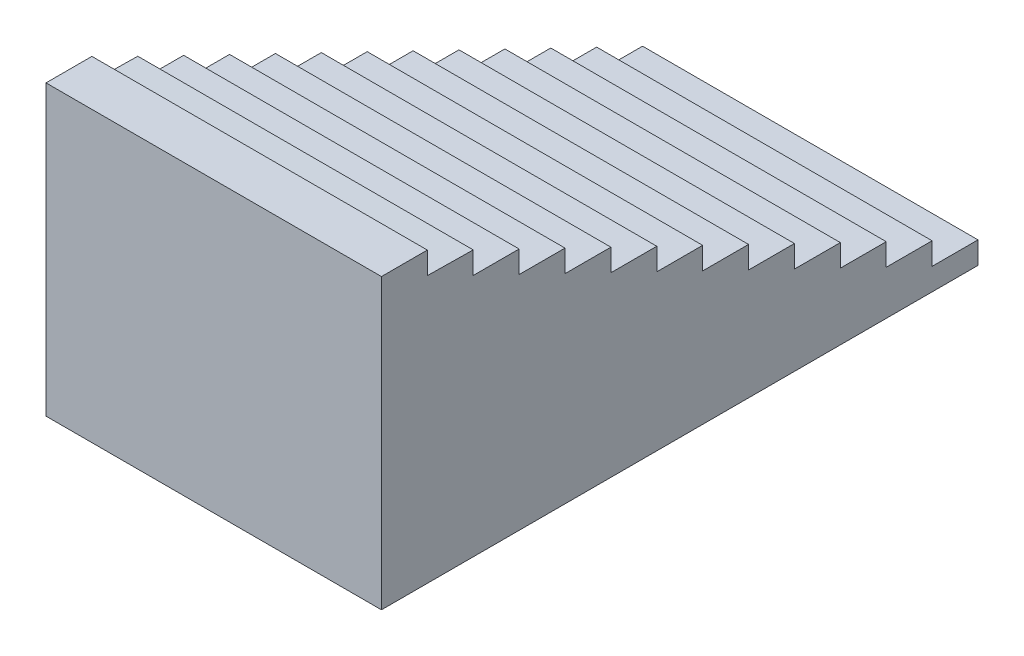
SolidWorks part; units mm, degrees
ref_plane "Front Plane" through (0, 0, 0) normal (0, 0, 1) x (1, 0, 0)
ref_plane "Top Plane" through (0, 0, 0) normal (0, 1, 0) x (1, 0, 0)
ref_plane "Right Plane" through (0, 0, 0) normal (1, 0, 0) x (0, 0, -1)
sketch "Sketch1" plane through (0, 0, 0) normal (1, 0, 0) x (0, 0, -1)
  line L0 (-350, 195.2131) -> (-60, 195.2131)
  line L1 (-60, 195.2131) -> (-60, 55.2131)
  line L2 (-60, 55.2131) -> (229.9707, 51.0927)
  line L7 (229.9707, 51.0927) -> (229.9707, -88.9073)
  line L8 (229.9707, -88.9073) -> (519.9707, -88.9073)
  line L9 (519.9707, -88.9073) -> (519.9707, -228.9073)
  line L10 (519.9707, -228.9073) -> (809.9707, -228.9073)
  line L11 (809.9707, -228.9073) -> (809.9707, -368.9073)
  line L12 (809.9707, -368.9073) -> (1099.9707, -368.9073)
  line L13 (1099.9707, -368.9073) -> (1099.9707, -508.9073)
  line L14 (1099.9707, -508.9073) -> (1389.9707, -508.9073)
  line L15 (1389.9707, -508.9073) -> (1389.9707, -648.9073)
  line L16 (1389.9707, -648.9073) -> (1679.9707, -648.9073)
  line L17 (1679.9707, -648.9073) -> (1679.9707, -788.9073)
  line L18 (1679.9707, -788.9073) -> (1969.9707, -788.9073)
  line L19 (1969.9707, -788.9073) -> (1969.9707, -928.9073)
  line L20 (1969.9707, -928.9073) -> (2259.9707, -928.9073)
  line L21 (2259.9707, -928.9073) -> (2259.9707, -1068.9073)
  line L22 (2259.9707, -1068.9073) -> (2549.9707, -1068.9073)
  line L23 (2549.9707, -1068.9073) -> (2549.9707, -1208.9073)
  line L24 (2549.9707, -1208.9073) -> (2839.9707, -1208.9073)
  line L25 (2839.9707, -1208.9073) -> (2839.9707, -1348.9073)
  line L26 (2839.9707, -1348.9073) -> (3129.9707, -1348.9073)
  line L27 (3129.9707, -1348.9073) -> (3129.9707, -1488.9073)
  line L28 (3129.9707, -1488.9073) -> (3419.9707, -1488.9073)
  line L29 (3419.9707, -1488.9073) -> (3419.9707, -1628.9073)
  line L30 (-350, 195.2131) -> (-350, -1628.9073)
  line L31 (-350, 195.2131) -> (3419.9707, 195.2131) construction
  line L32 (-350, 195.2131) -> (-350, -1628.9073) construction
  line L33 (-350, -1628.9073) -> (3419.9707, -1628.9073) construction
  line L34 (3419.9707, 195.2131) -> (3419.9707, -1628.9073) construction
  line L35 (-350, -1628.9073) -> (3419.9707, -1628.9073)
  point P4 (0, 0)
  dimension "D3" = 290
  dimension "D4" = 140
extrude "Boss-Extrude1" add sketch "Sketch1" against normal blind 2120
